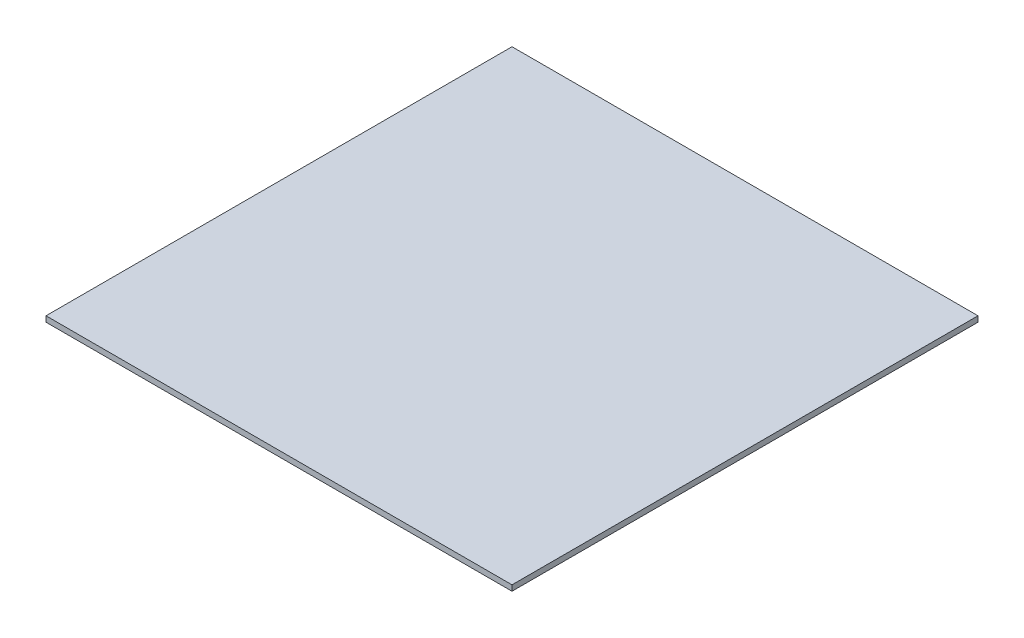
SolidWorks part; units mm, degrees
ref_plane "Front Plane" through (0, 0, 0) normal (0, 0, 1) x (1, 0, 0)
ref_plane "Top Plane" through (0, 0, 0) normal (0, 1, 0) x (1, 0, 0)
ref_plane "Right Plane" through (0, 0, 0) normal (1, 0, 0) x (0, 0, -1)
sketch "Sketch1" plane through (0, 0, 0) normal (0, 1, 0) x (1, 0, 0)
  line L1 (-495.3, -495.3) -> (495.3, -495.3)
  line L2 (-495.3, -495.3) -> (-495.3, 495.3)
  line L3 (-495.3, 495.3) -> (495.3, 495.3)
  line L4 (495.3, -495.3) -> (495.3, 495.3)
  line L5 (-495.3, -495.3) -> (495.3, 495.3) construction
  line L6 (-495.3, 495.3) -> (495.3, -495.3) construction
  point P0 (0, 0)
  dimension "D1" = 990.6
  dimension "D2" = 990.6
extrude "Boss-Extrude1" add sketch "Sketch1" along normal blind 11.9062
